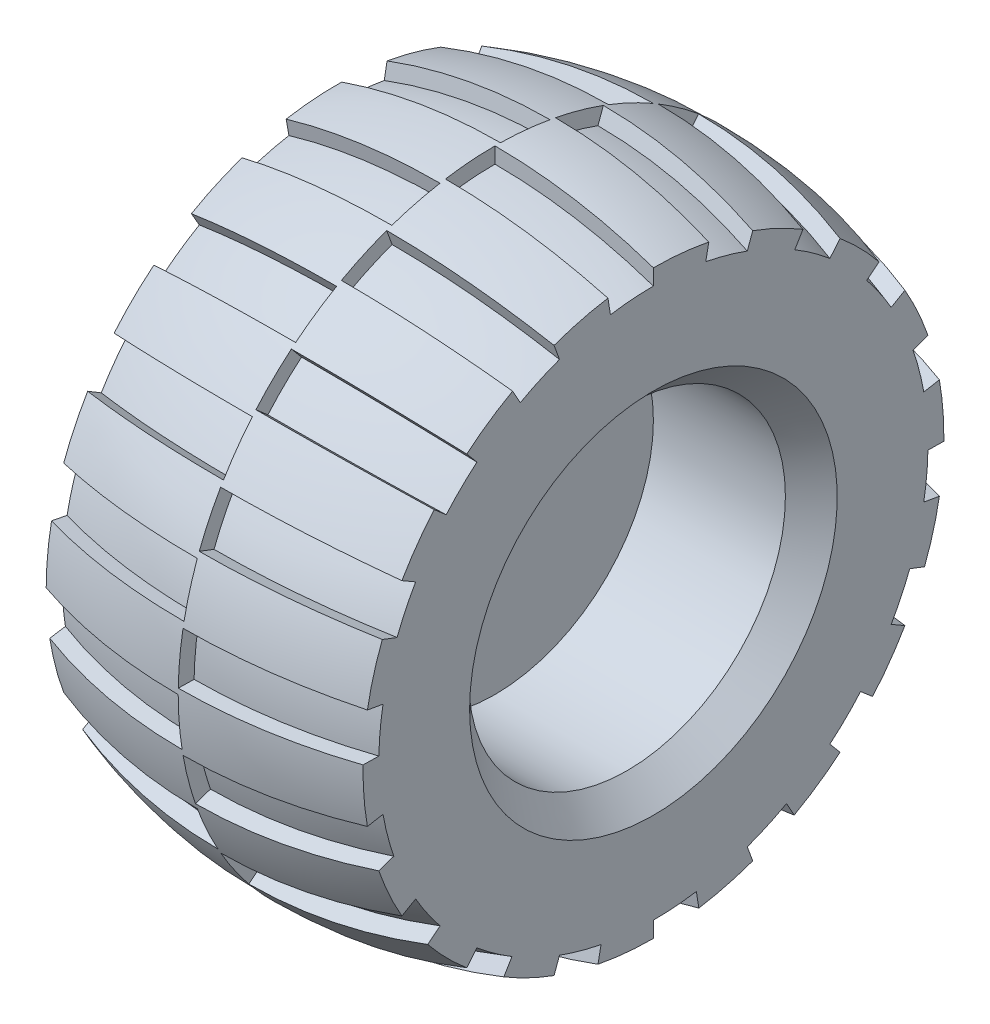
SolidWorks part; units mm, degrees
ref_plane "Front Plane" through (0, 0, 0) normal (0, 0, 1) x (1, 0, 0)
ref_plane "Top Plane" through (0, 0, 0) normal (0, 1, 0) x (1, 0, 0)
ref_plane "Right Plane" through (0, 0, 0) normal (1, 0, 0) x (0, 0, -1)
ref_axis "Axis1" through (-40.6149, 0, 0) along (1, 0, 0)
sketch "Sketch1" plane through (0, 0, 0) normal (0, 0, 1) x (1, 0, 0)
  line L0 (-25, 30) -> (25, 30)
  line L1 (25, 30) -> (30, 34.8133)
  line L2 (30, 34.8133) -> (30, 55)
  line L3 (-25, 30) -> (-30, 34.8133)
  line L4 (-30, 34.8133) -> (-30, 55)
  line L5 (0, 0) -> (0, 37004.8058) construction
  line L6 (-30, 55) -> (30, 55) construction
  line L7 (-30, 34.8133) -> (30, 34.8133) construction
  line L8 (-7.5205, 60) -> (49992.4795, 60) construction
  arc A0 (-30, 55) -> (30, 55) centre (0, -32.5) cw
  dimension "D1" = 30
  dimension "D2" = 60
  dimension "D3" = 60
  dimension "D4" = 55
  dimension "D5" = 5
revolve "Revolve1" add sketch "Sketch1" angle 360 about axis through (-40.6149, 0, 0) along (1, 0, 0)
sketch "Sketch2" plane through (0, 0, 0) normal (0, 0, 1) x (1, 0, 0)
  line L0 (0, 60) -> (0, 57)
  line L1 (30, 55) -> (30, 52)
  line L2 (30, -55) -> (30, 55) construction
  arc A0 (30, 55) -> (-30, 55) centre (0, -32.5) ccw construction
  arc A1 (0, 60) -> (30, 55) centre (0, -32.5) cw
  arc A2 (0, 57) -> (30, 52) centre (0, -35.5) cw
  dimension "D1" = 3
revolve "Cut-Revolve2" cut sketch "Sketch2" angle 9 about axis through (-40.6149, 0, 0) along (1, 0, 0)
ref_plane "Plane1" through (0, 0, 0) normal (0, 0.0175, 0.9998) x (1, 0, 0)
pattern_circular "CirPattern2" count 18 over 360 about axis through (0, 0, 0) along (1, 0, 0) of "Cut-Revolve2"
sketch "Sketch5" plane through (0, 0, 0) normal (0, 0.0175, 0.9998) x (1, 0, 0)
  line L0 (-30, 55) -> (-30, 52)
  line L1 (-30, 55) -> (-30, -55) construction
  line L2 (0, 60) -> (0, 57)
  arc A0 (0, 60) -> (-30, 55) centre (0, -32.5) ccw
  arc A1 (0, 57) -> (-30, 52) centre (0, -35.5) ccw
  arc A2 (30, 55) -> (-30, 55) centre (0, -32.5) ccw construction
  dimension "D1" = 3
revolve "Cut-Revolve3" cut sketch "Sketch5" angle 9 about axis through (-40.6149, 0, 0) along (1, 0, 0)
pattern_circular "CirPattern3" count 18 over 360 about axis through (0, 0, 0) along (1, 0, 0) of "Cut-Revolve3"
sketch "Sketch9" plane through (0, 0, 0) normal (1, 0, 0) x (0, 0, -1)
  circle A0 centre (0, 0) radius 30
  circle A1 centre (0, 0) radius 30 construction
extrude "Boss-Extrude2" add sketch "Sketch9" against normal blind 25
sketch "Sketch10" plane through (-25, 0, 0) normal (-1, 0, 0) x (0, 0, 1)
  circle A0 centre (0, 0) radius 5
  dimension "D1" = 10
extrude "Boss-Extrude3" add sketch "Sketch10" along normal blind 14
